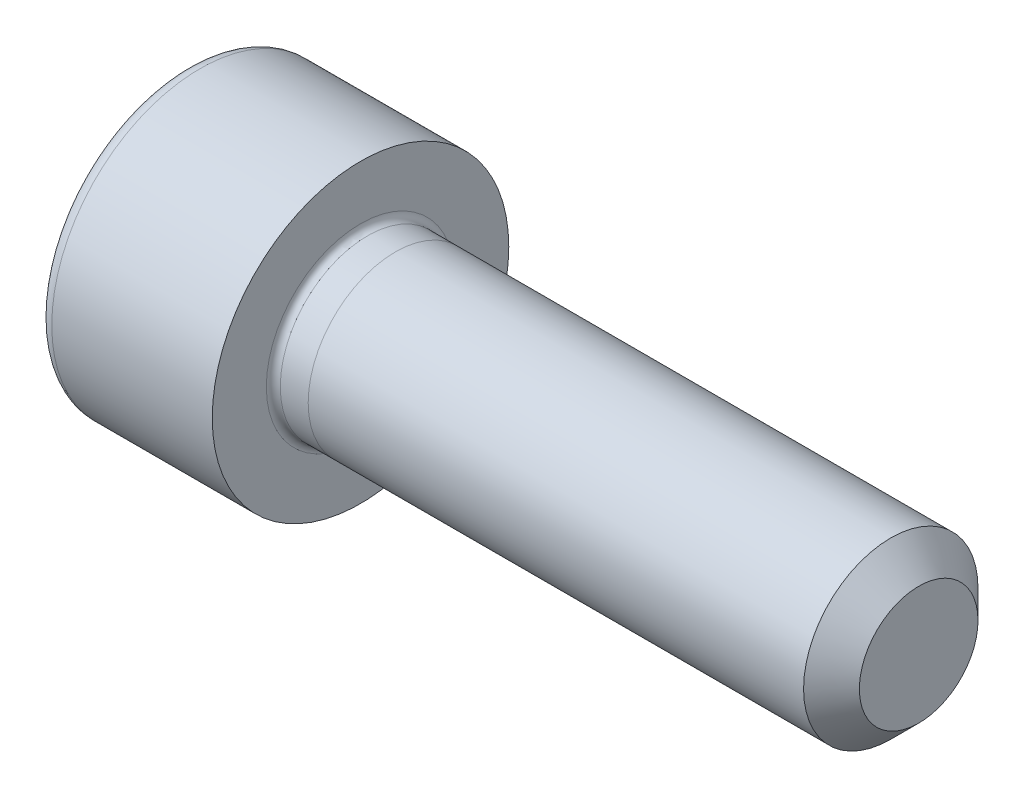
SolidWorks part; units mm, degrees
ref_plane "Спереди" through (0, 0, 0) normal (0, 0, 1) x (1, 0, 0)
ref_plane "Сверху" through (0, 0, 0) normal (0, 1, 0) x (1, 0, 0)
ref_plane "Справа" through (0, 0, 0) normal (1, 0, 0) x (0, 0, -1)
sketch "Эскиз1" plane through (0, 0, 0) normal (1, 0, 0) x (0, 0, -1)
  circle A0 centre (0, 0) radius 2.5
  dimension "D1" = 5
extrude "Вытянуть1" add sketch "Эскиз1" along normal blind 16
sketch "Эскиз2" plane through (0, 0, 0) normal (-1, 0, 0) x (0, 0, 1)
  circle A0 centre (0, 0) radius 4.25
  dimension "D1" = 8.5
extrude "Вытянуть2" add sketch "Эскиз2" along normal blind 5
sketch "Эскиз3" plane through (-5, 0, 0) normal (-1, 0, 0) x (0, 0, 1)
  circle A0 centre (0, 0) radius 2
  dimension "D1" = 4
extrude "Вырез-Вытянуть1" cut sketch "Эскиз3" against normal blind 3.4
chamfer "Фаска1" distance 0.8 angle 45 1 edges at (16, 0, -2.5)
fillet "Скругление1" radius 0.4 1 edges at (-5, 0, 4.25)
fillet "Скругление2" radius 0.2 1 edges at (0, 0, 2.5)
chamfer "Фаска2" distance 0.4 angle 30 1 edges at (-5, 0, 2)
sketch "Эскиз4" plane through (-5, 0, 0) normal (-1, 0, 0) x (0, 0, 1)
  line L1 (2.3094, 0) -> (1.1547, 2)
  line L2 (1.1547, 2) -> (-1.1547, 2)
  line L3 (-1.1547, 2) -> (-2.3094, 0)
  line L4 (-2.3094, 0) -> (-1.1547, -2)
  line L5 (-1.1547, -2) -> (1.1547, -2)
  line L6 (1.1547, -2) -> (2.3094, 0)
  circle A0 centre (0, 0) radius 2 construction
  dimension "D1" = 4
extrude "Вырез-Вытянуть2" cut sketch "Эскиз4" against normal blind 2.8
sketch "Эскиз5" plane through (0, 0, 0) normal (0, 0, 1) x (1, 0, 0)
  line L0 (1, 9.975) -> (1, -10.8696)
  line L1 (16, -1.7) -> (16, 1.7) construction
  dimension "D1" = 15
split line "Разделяющая линия1"
